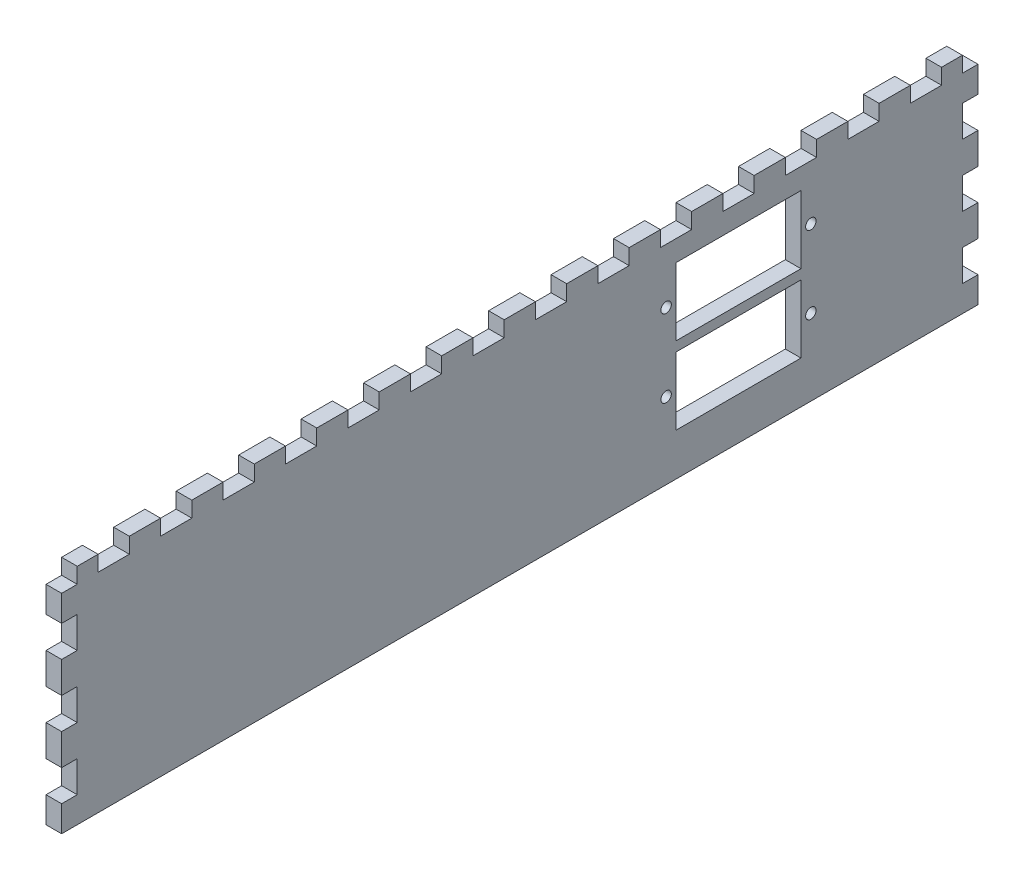
SolidWorks part; units mm, degrees
material "Acrylic (Medium-high impact)"
ref_plane "Front Plane" through (0, 0, 0) normal (0, 0, 1) x (1, 0, 0)
ref_plane "Top Plane" through (0, 0, 0) normal (0, 1, 0) x (1, 0, 0)
ref_plane "Right Plane" through (0, 0, 0) normal (1, 0, 0) x (0, 0, -1)
sketch "Sketch1" plane through (0, 0, 0) normal (1, 0, 0) x (0, 0, -1)
  line L1 (-85, 20) -> (85, 20)
  line L2 (-85, 20) -> (-85, -20)
  line L3 (-85, -20) -> (85, -20)
  line L4 (85, 20) -> (85, -20)
  line L5 (-85, 20) -> (85, -20) construction
  line L6 (-85, -20) -> (85, 20) construction
  point P0 (0, 0)
  dimension "D1" = 170
  dimension "D2" = 40
extrude "Boss-Extrude1" add sketch "Sketch1" along normal blind 3
sketch "Sketch3" plane through (0, 0, -85) normal (0, 0, -1) x (-1, 0, 0)
  line L0 (0, 0) -> (-3, 0) construction
  line L1 (0, -20) -> (0, 20) construction
  line L2 (-3, -20) -> (-3, 20) construction
  line L4 (0, 3) -> (-3, 3)
  line L5 (0, 3) -> (0, 9)
  line L6 (0, 9) -> (-3, 9)
  line L7 (-3, 3) -> (-3, 9)
  line L8 (0, 3) -> (-3, 9) construction
  line L9 (0, 9) -> (-3, 3) construction
  point P10 (-1.5, 6)
  dimension "D1" = 3
  dimension "D2" = 6
extrude "Boss-Extrude2" add sketch "Sketch3" along normal blind 3
pattern_linear "LPattern1" count 3 spacing 12 along (0, -1, 0) count 2 spacing 12 along (0, 1, 0) of "Boss-Extrude2"
ref_plane "Plane1" [suppressed] through (0, -20, 0) normal (0, -1, 0) x (-1, 0, 0)
sketch "Sketch4" plane through (0, 20, 0) normal (0, 1, 0) x (1, 0, 0)
  line L0 (0, 0) -> (3, 0) construction
  line L1 (0, 85) -> (0, -85) construction
  line L2 (3, 85) -> (3, -85) construction
  line L4 (0, -3) -> (3, -3)
  line L5 (0, -3) -> (0, 3)
  line L6 (0, 3) -> (3, 3)
  line L7 (3, -3) -> (3, 3)
  line L8 (0, -3) -> (3, 3) construction
  line L9 (0, 3) -> (3, -3) construction
  point P7 (1.5, 0)
  dimension "D1" = 6
extrude "Boss-Extrude3" add sketch "Sketch4" along normal blind 3
pattern_linear "LPattern2" count 8 spacing 12 along (0, 0, -1) count 8 spacing 12 along (0, 0, 1) of "Boss-Extrude3"
ref_plane "Plane2" through (0, 0, 0) normal (0, 0, 1) x (1, 0, 0)
sketch "Sketch5" [suppressed] plane through (0, 0, 0) normal (-1, 0, 0) x (0, 0, 1)
  line L0 (-88, -21) -> (-88, -15) construction
  line L1 (-75, 19) -> (-88, 19)
  line L2 (-75, 19) -> (-75, 21)
  line L3 (-75, 21) -> (-88, 21)
  line L4 (-88, 19) -> (-88, 21)
  line L5 (-75, 19) -> (-88, 21) construction
  line L6 (-75, 21) -> (-88, 19) construction
  line L7 (-85, -21) -> (-88, -21)
  line L8 (-85, -21) -> (-85, -20)
  line L9 (-85, -20) -> (-88, -20)
  line L10 (-88, -21) -> (-88, -20)
  line L11 (-85, -21) -> (-88, -20) construction
  line L12 (-85, -20) -> (-88, -21) construction
  line L13 (85, -20) -> (-85, -20) construction
  point P4 (-81.5, 20)
  point P11 (-86.5, -20.5)
mirror "Mirror1" about plane through (0, 0, 0) normal (0, 0, 1) of "LPattern1", "Boss-Extrude2"
sketch "Sketch6" plane through (3, 0, 0) normal (1, 0, 0) x (0, 0, -1)
  line L0 (42, 1.1318) -> (42, -11.8682) construction
  line L1 (30, 1.1318) -> (54, 1.1318)
  line L2 (30, 1.1318) -> (30, -11.8682)
  line L3 (30, -11.8682) -> (54, -11.8682)
  line L4 (54, 1.1318) -> (54, -11.8682)
  line L5 (30, 1.1318) -> (54, -11.8682) construction
  line L6 (30, -11.8682) -> (54, 1.1318) construction
  line L7 (42, 15.9942) -> (42, 2.9942) construction
  line L8 (30, 15.9942) -> (54, 15.9942)
  line L9 (30, 15.9942) -> (30, 2.9942)
  line L10 (30, 2.9942) -> (54, 2.9942)
  line L11 (54, 15.9942) -> (54, 2.9942)
  line L12 (30, 15.9942) -> (54, 2.9942) construction
  line L13 (30, 2.9942) -> (54, 15.9942) construction
  line L14 (-85, -9) -> (-85, -15) construction
  circle A0 centre (28.1, -5.3682) radius 1
  circle A1 centre (55.9, -5.3682) radius 1
  circle A2 centre (28.1, 9.4942) radius 1
  circle A3 centre (55.9, 9.4942) radius 1
  point P9 (42, -5.3682)
  point P11 (42, -5.3682)
  point P21 (42, 9.4942)
  point P23 (42, 9.4942)
  dimension "D1" = 2
  dimension "D5" = 2
  dimension "D2" = 27.8
  dimension "D4" = 13
  dimension "D7" = 24
  dimension "D8" = 13
  dimension "D9" = 115
extrude "Cut-Extrude2" cut sketch "Sketch6" against normal through all
sketch "Sketch7" plane through (3, 0, 0) normal (1, 0, 0) x (0, 0, -1)
  line L0 (88, 20) -> (85, 20)
  line L1 (88, 21) -> (88, 15) construction
  line L2 (85, 20) -> (85, 23)
  line L3 (81, 23) -> (87, 23) construction
  line L4 (88, 20) -> (88, 23)
  line L5 (88, 23) -> (85, 23)
  dimension "D1" = 3
  dimension "D2" = 3
extrude "Cut-Extrude4" cut sketch "Sketch7" along direction (-1, 0, 0) on the side against the normal through all
mirror "Mirror2" about plane through (0, 0, 0) normal (0, 0, 1) of "Cut-Extrude4"
sketch "Sketch8" plane through (0, 0, 0) normal (-1, 0, 0) x (0, 0, 1)
  line L1 (85, -20) -> (88, -20)
  line L2 (85, -20) -> (85, -21)
  line L3 (85, -21) -> (88, -21)
  line L4 (88, -20) -> (88, -21)
  line L5 (85, -20) -> (88, -21) construction
  line L6 (85, -21) -> (88, -20) construction
  point P4 (86.5, -20.5)
extrude "Cut-Extrude5" cut sketch "Sketch8" against normal up to next (3 mm away)
mirror "Mirror3" about plane through (0, 0, 0) normal (0, 0, 1) of "Cut-Extrude5"
